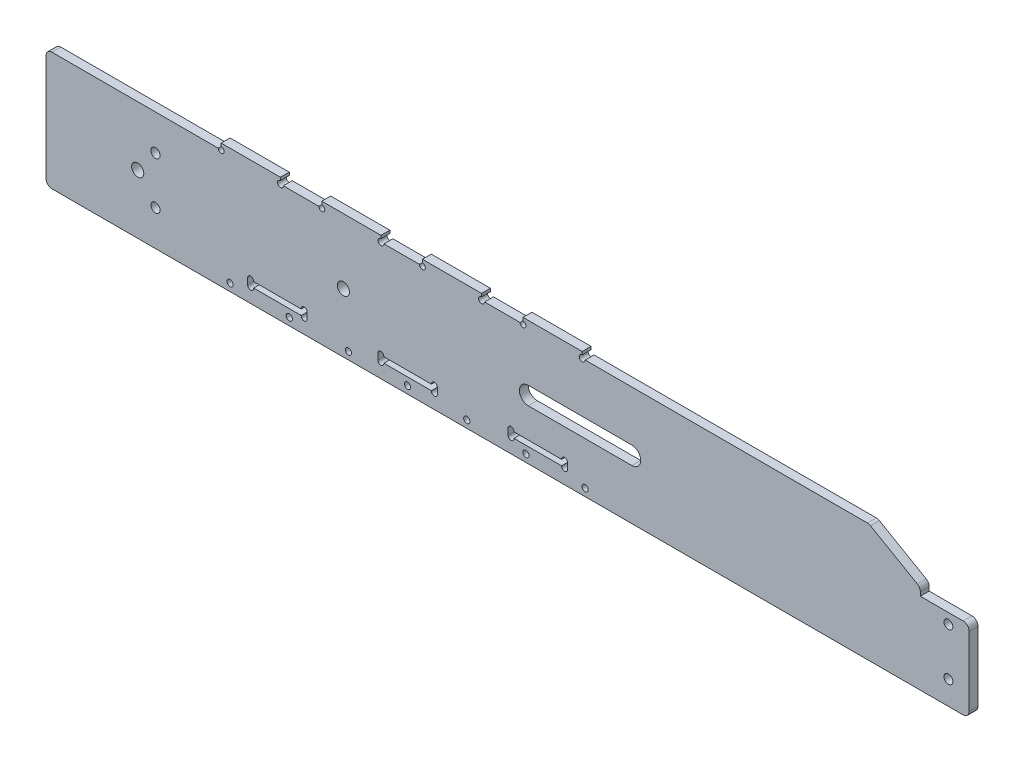
SolidWorks part; units mm, degrees
material "Thornel Mat VMA"
ref_plane "前视基准面" through (0, 0, 0) normal (0, 0, 1) x (1, 0, 0)
ref_plane "上视基准面" through (0, 0, 0) normal (0, 1, 0) x (1, 0, 0)
ref_plane "右视基准面" through (0, 0, 0) normal (1, 0, 0) x (0, 0, -1)
sketch "草图1" plane through (0, 0, 0) normal (0, 0, 1) x (1, 0, 0)
  line L1 (-180, -20) -> (180, -20)
  line L2 (-180, -20) -> (-180, 20)
  line L3 (-180, 20) -> (180, 20)
  line L4 (180, -20) -> (180, 20)
  line L5 (-180, -20) -> (180, 20) construction
  line L6 (-180, 20) -> (180, -20) construction
  point P0 (0, 0)
  dimension "D1" = 360
  dimension "D2" = 40
extrude "凸台-拉伸1" add sketch "草图1" along normal blind 3
sketch "草图2" plane through (0, 0, 0) normal (0, 0, 1) x (1, 0, 0)
  line L0 (-157.1827, 0) -> (155.6526, 0) construction
  line L1 (-180, -20) -> (-196, -20)
  line L2 (-180, -20) -> (-180, 7.5)
  line L3 (-180, 7.5) -> (-196, 7.5)
  line L4 (-196, -20) -> (-196, 7.5)
  line L5 (180, -20) -> (196, -20)
  line L6 (180, -20) -> (180, 7.5)
  line L7 (180, 7.5) -> (196, 7.5)
  line L8 (196, -20) -> (196, 7.5)
  dimension "D1" = 16
  dimension "D2" = 16
  dimension "D3" = 27.5
  dimension "D4" = 27.5
extrude "凸台-拉伸2" add sketch "草图2" along normal blind 3
sketch "草图3" plane through (0, 0, 3) normal (0, 0, 1) x (1, 0, 0)
  line L0 (-180, 20) -> (-180, 7.5) construction
  line L1 (-212.4147, 0) -> (176.0969, 0) construction
  line L2 (0, -57.7717) -> (0, 69.9209) construction
  line L3 (212.4147, 0) -> (-176.0969, 0) construction
  line L7 (-212.4147, 0) -> (176.0969, 0) construction
  line L8 (212.4147, 0) -> (-176.0969, 0) construction
  circle A0 centre (-189, -12) radius 1.5
  circle A1 centre (-189, 4) radius 1.5
  circle A4 centre (-145, 0) radius 4.5
  circle A7 centre (189, 4) radius 1.5
  circle A8 centre (189, -12) radius 1.5
  circle A9 centre (72, 0) radius 3
  dimension "D1" = 3
  dimension "D2" = 3
  dimension "D7" = 9
  dimension "D9" = 217
  dimension "D8" = 6
  dimension "D3" = 9
  dimension "D4" = 16
  dimension "D5" = 4
  dimension "D6" = 44
extrude "切除-拉伸1" cut sketch "草图3" against normal through all
sketch "草图6" plane through (0, 0, 3) normal (0, 0, 1) x (1, 0, 0)
  line L0 (-180, 7.5) -> (-196, 7.5) construction
  line L1 (-180, 20) -> (-179.5, 20)
  line L2 (-180, 20) -> (-180, 7.5)
  line L3 (-180, 7.5) -> (-179.5, 7.5)
  line L4 (-179.5, 20) -> (-179.5, 7.5)
  line L5 (180, 20) -> (179.5, 20)
  line L6 (180, 20) -> (180, 7.5)
  line L7 (180, 7.5) -> (179.5, 7.5)
  line L8 (179.5, 20) -> (179.5, 7.5)
  line L9 (196, 7.5) -> (180, 7.5) construction
  dimension "D1" = 0.5
  dimension "D2" = 0.5
  dimension "D3" = 0
  dimension "D4" = 0
extrude "切除-拉伸4" cut sketch "草图6" against normal blind 10
sketch "草图13" plane through (0, 0, 3) normal (0, 0, 1) x (1, 0, 0)
  line L0 (47, 0) -> (82, 0) construction
  line L1 (47, 3) -> (82, 3)
  line L2 (47, -3) -> (82, -3)
  arc A0 (47, 3) -> (47, -3) centre (47, 0) ccw
  arc A1 (82, -3) -> (82, 3) centre (82, 0) ccw
  circle A2 centre (72, 0) radius 3 construction
  point P3 (64.5, 0)
  dimension "D1" = 3
  dimension "D2" = 10
  dimension "D3" = 25
extrude "切除-拉伸10" cut sketch "草图13" against normal blind 10
sketch "草图14" plane through (0, 0, 3) normal (0, 0, 1) x (1, 0, 0)
  line L0 (-116, 20) -> (-116, -20)
  line L1 (179.5, 20) -> (-179.5, 20) construction
  line L2 (-196, -20) -> (196, -20) construction
  line L3 (-116, -20) -> (-196, -20)
  line L4 (-196, -20) -> (-196, 20)
  line L5 (-196, 20) -> (-116, 20)
  dimension "D1" = 80
extrude "切除-拉伸11" cut sketch "草图14" against normal blind 10
sketch "草图15" plane through (0, 0, 3) normal (0, 0, 1) x (1, 0, 0)
  line L0 (-62.2235, 0) -> (39.7809, 0) construction
  line L1 (-116, -20) -> (196, -20) construction
  line L2 (-116, -20) -> (-116, 20) construction
  line L3 (0, 0) -> (0, -20) construction
  line L4 (-15.5, 0) -> (-15.5, -4.9483) construction
  circle A0 centre (-85, 0) radius 2.05
  circle A1 centre (0, 0) radius 2.05 construction
  circle A4 centre (54, 0) radius 2.05
  circle A5 centre (-15.5, 0) radius 2.05
  dimension "D2" = 4.1
  dimension "D5" = 4.1
  dimension "D1" = 20
  dimension "D3" = 31
  dimension "D4" = 54
extrude "切除-拉伸12" cut sketch "草图15" against normal blind 10
sketch "草图16" plane through (0, 0, 0) normal (0, 0, -1) x (-1, 0, 0)
  circle A0 centre (-66.215, -17.5) radius 1.05
  circle A1 centre (-46.215, -17.5) radius 1.05
  circle A2 centre (-26.215, -17.5) radius 1.05
  circle A3 centre (-6.215, -17.5) radius 1.05
  circle A4 centre (13.785, -17.5) radius 1.05
  circle A5 centre (33.785, -17.5) radius 1.05
  circle A6 centre (53.785, -17.5) radius 1.05
  dimension "D1" = 2.1
extrude "切除-拉伸13" cut sketch "草图16" against normal blind 10
sketch "草图17" plane through (0, 0, 0) normal (0, 0, -1) x (-1, 0, 0)
  line L0 (-65.215, 20) -> (-65.215, 22)
  line L1 (-179.5, 20) -> (116, 20) construction
  line L2 (-65.215, 22) -> (-45.215, 22)
  line L3 (-45.215, 22) -> (-45.215, 20)
  line L4 (-45.215, 20) -> (-65.215, 20)
  line L5 (-75.215, 22) -> (-75.215, 20) construction
  line L6 (-21.215, 22) -> (-21.215, 7.5304) construction
  line L7 (-73.215, 22) -> (30.785, 22) construction
  line L9 (-11.215, 20) -> (-31.215, 20)
  line L10 (-31.215, 20) -> (-31.215, 22)
  line L11 (-31.215, 22) -> (-11.215, 22)
  line L12 (-11.215, 22) -> (-11.215, 20)
  line L13 (2.785, 20) -> (22.785, 20)
  line L14 (2.785, 22) -> (2.785, 20)
  line L15 (22.785, 22) -> (2.785, 22)
  line L16 (22.785, 20) -> (22.785, 22)
  line L17 (36.785, 20) -> (56.785, 20)
  line L18 (56.785, 22) -> (36.785, 22)
  line L19 (36.785, 22) -> (36.785, 20)
  line L20 (56.785, 20) -> (56.785, 22)
  dimension "D1" = 10
  dimension "D2" = 20
  dimension "D3" = 2
  dimension "D5" = 10
  dimension "D6" = 2
  dimension "D7" = 14
  dimension "D4" = 2
extrude "凸台-拉伸3" add sketch "草图17" against normal blind 3
sketch "草图18" plane through (0, 0, 0) normal (0, 0, -1) x (-1, 0, 0)
  line L0 (27.735, -12.95) -> (47.835, -12.95)
  line L1 (-60.265, -12.95) -> (-40.165, -12.95)
  line L2 (-60.265, -12.95) -> (-60.265, -15.05)
  line L3 (-60.265, -15.05) -> (-40.165, -15.05)
  line L4 (-40.165, -12.95) -> (-40.165, -15.05)
  line L5 (-60.265, -12.95) -> (-40.165, -15.05) construction
  line L6 (-60.265, -15.05) -> (-40.165, -12.95) construction
  line L7 (27.735, -15.05) -> (47.835, -15.05)
  line L8 (-40.165, -12.95) -> (-40.165, -15.05) construction
  line L9 (47.835, -12.95) -> (47.835, -15.05)
  line L13 (-16.265, -12.95) -> (3.835, -12.95)
  line L14 (-16.265, -15.05) -> (3.835, -15.05)
  line L15 (3.835, -12.95) -> (3.835, -15.05)
  line L16 (-16.265, -12.95) -> (-16.265, -15.05)
  line L17 (27.735, -12.95) -> (27.735, -15.05)
  point P0 (-50.215, -14)
  dimension "D2" = 44
extrude "切除-拉伸14" cut sketch "草图18" against normal through all
sketch "草图19" plane through (0, 0, 0) normal (0, 0, -1) x (-1, 0, 0)
  line L0 (-40.165, -12.95) -> (-60.265, -12.95) construction
  line L1 (-60.265, -15.05) -> (-40.165, -15.05) construction
  circle A0 centre (-59.265, -12.95) radius 1
  circle A1 centre (-59.265, -15.05) radius 1
  circle A2 centre (-41.165, -12.95) radius 1
  circle A3 centre (-41.165, -15.05) radius 1
  circle A4 centre (-15.265, -12.95) radius 1
  circle A5 centre (-15.265, -15.05) radius 1
  circle A6 centre (2.835, -12.95) radius 1
  circle A7 centre (2.835, -15.05) radius 1
  circle A8 centre (28.735, -12.95) radius 1
  circle A9 centre (28.735, -15.05) radius 1
  circle A10 centre (46.835, -12.95) radius 1
  circle A11 centre (46.835, -15.05) radius 1
  dimension "D1" = 2
  dimension "D3" = 44
  dimension "D2" = 3
extrude "切除-拉伸15" cut sketch "草图19" against normal blind 3
chamfer "倒角1" distance 10 angle 60 1 edges at (179.5, 20, 1.5)
fillet "圆角2" radius 2 6 edges at (-116, 20, 1.5) (-116, -20, 1.5) (162.1795, 20, 1.5) (179.5, 10, 1.5) (196, 7.5, 1.5) (196, -20, 1.5)
sketch "草图22" plane through (0, 0, 0) normal (0, 0, -1) x (-1, 0, 0)
  line L0 (79, 20) -> (79, -12.95) construction
  line L1 (22.785, 20) -> (36.785, 20) construction
  line L2 (45.835, -12.95) -> (29.735, -12.95) construction
  circle A0 centre (85, 0) radius 2.05 construction
  circle A1 centre (79, 8) radius 1.55
  circle A2 centre (79, -8) radius 1.55
  dimension "D2" = 3.1
  dimension "D3" = 3.1
  dimension "D5" = 8
  dimension "D1" = 6
  dimension "D4" = 8
extrude "切除-拉伸17" cut sketch "草图22" against normal blind 10
sketch "草图24" plane through (0, 0, 0) normal (0, 0, -1) x (-1, 0, 0)
  line L0 (-58.265, -12.95) -> (-42.165, -12.95)
  line L1 (-58.265, -12.95) -> (-58.265, -13.05)
  line L2 (-42.165, -12.95) -> (-42.165, -13.05)
  line L3 (-58.265, -13.05) -> (-42.165, -13.05)
  line L4 (-58.265, -15.05) -> (-42.165, -15.05)
  line L5 (-58.265, -15.05) -> (-58.265, -14.95)
  line L6 (-42.165, -15.05) -> (-42.165, -14.95)
  line L7 (-58.265, -14.95) -> (-42.165, -14.95)
  line L8 (-14.265, -12.95) -> (1.835, -12.95)
  line L9 (-14.265, -12.95) -> (-14.265, -13.05)
  line L10 (1.835, -12.95) -> (1.835, -13.05)
  line L11 (-14.265, -13.05) -> (1.835, -13.05)
  line L12 (-14.265, -15.05) -> (1.835, -15.05)
  line L13 (-14.265, -15.05) -> (-14.265, -14.95)
  line L14 (1.835, -15.05) -> (1.835, -14.95)
  line L15 (-14.265, -14.95) -> (1.835, -14.95)
  line L16 (29.735, -12.95) -> (45.835, -12.95)
  line L17 (29.735, -12.95) -> (29.735, -13.05)
  line L18 (45.835, -12.95) -> (45.835, -13.05)
  line L19 (29.735, -13.05) -> (45.835, -13.05)
  line L20 (29.735, -15.05) -> (45.835, -15.05)
  line L21 (29.735, -15.05) -> (29.735, -14.95)
  line L22 (45.835, -15.05) -> (45.835, -14.95)
  line L23 (29.735, -14.95) -> (45.835, -14.95)
  line L24 (29.735, -15.05) -> (45.835, -15.05) construction
  arc A0 (29.735, -12.95) -> (27.735, -12.95) centre (28.735, -12.95) ccw construction
  arc A1 (27.735, -15.05) -> (29.735, -15.05) centre (28.735, -15.05) ccw construction
  dimension "D1" = 0.1
  dimension "D2" = 0.1
  dimension "D3" = 0.1
  dimension "D4" = 0.1
  dimension "D5" = 0.1
  dimension "D6" = 0.1
extrude "凸台-拉伸4" add sketch "草图24" against normal up to surface (3 mm away) up to face at (-80.55, 8, 3)
sketch "草图25" plane through (0, 0, 0) normal (0, 0, -1) x (-1, 0, 0)
  circle A0 centre (-65.215, 20) radius 1
  circle A1 centre (-45.215, 20) radius 1
  circle A2 centre (-31.215, 20) radius 1
  circle A3 centre (-11.215, 20) radius 1
  circle A4 centre (2.785, 20) radius 1
  circle A5 centre (22.785, 20) radius 1
  circle A6 centre (36.785, 20) radius 1
  circle A7 centre (56.785, 20) radius 1
  dimension "D1" = 2
  dimension "D2" = 2
  dimension "D3" = 2
  dimension "D4" = 2
  dimension "D5" = 2
  dimension "D6" = 2
  dimension "D7" = 2
  dimension "D8" = 2
extrude "切除-拉伸18" cut sketch "草图25" against normal blind 10
